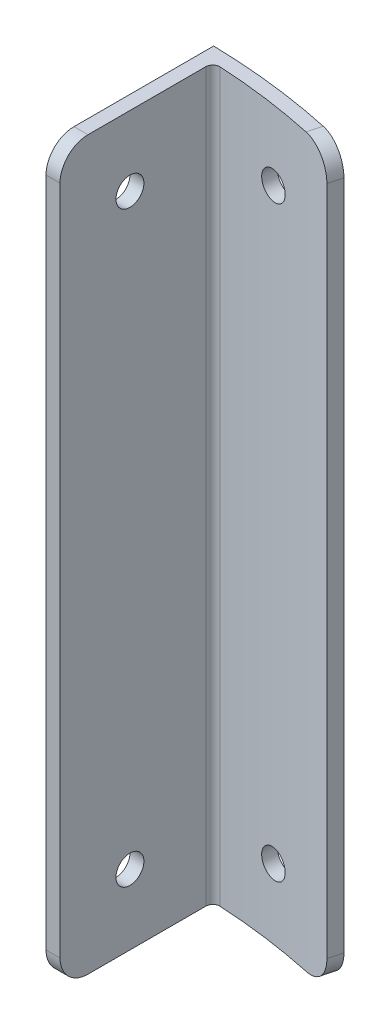
SolidWorks part; units mm, degrees
material "6061-T6 (SS)"
ref_plane "Front Plane" through (0, 0, 0) normal (0, 0, 1) x (1, 0, 0)
ref_plane "Top Plane" through (0, 0, 0) normal (0, 1, 0) x (1, 0, 0)
ref_plane "Right Plane" through (0, 0, 0) normal (1, 0, 0) x (0, 0, -1)
sketch "Sketch1" plane through (0, 0, 0) normal (0, 1, 0) x (1, 0, 0)
  line L0 (0, 149.225) -> (0, 0)
  line L1 (3.302, 111.125) -> (6.477, 111.125)
  line L2 (0, 149.225) -> (3.302, 149.225)
  line L3 (0, 149.225) -> (0, 111.125)
  line L4 (0, 111.125) -> (3.302, 111.125)
  line L5 (3.302, 149.225) -> (3.302, 111.125)
  line L6 (6.477, 111.125) -> (6.477, 145.9063)
  line L7 (0, 0) -> (37.6874, 144.3875)
  circle A0 centre (0, 0) radius 149.225
  circle A1 centre (0, 0) radius 146.05
  arc A2 (36.8855, 141.3155) -> (6.477, 145.9063) centre (0, 0) ccw
  circle A3 centre (0, 0) radius 146.05
  circle A4 centre (0, 0) radius 149.225
  dimension "D1" = 298.45
  dimension "D2" = 38.1
  dimension "D3" = 3.302
  dimension "D5" = 3.175
  dimension "D6" = 149.225
  dimension "D7" = 14.629
  dimension "D4" = 3.175
extrude "Boss-Extrude1" add sketch "Sketch1" along normal blind 165.1
fillet "Fillet1" radius 6.35 4 edges at (4.8895, 0, -111.125) (4.8895, 165.1, -111.125) (37.2865, 165.1, -142.8515) (37.2865, 0, -142.8515)
fillet "Fillet2" radius 1.5875 1 edges at (6.477, 82.55, -145.9063)
sketch "Sketch2" plane through (3.302, 0, 0) normal (-1, 0, 0) x (0, 0, 1)
  line L4 (-149.1885, 0) -> (-117.475, 0)
  line L5 (-111.125, 6.35) -> (-111.125, 158.75)
  line L6 (-117.475, 165.1) -> (-149.1885, 165.1)
  line L7 (-149.1885, 165.1) -> (-149.1885, 0)
  line L8 (-149.1885, 0) -> (-117.475, 0)
  line L9 (-111.125, 6.35) -> (-111.125, 158.75)
  line L10 (-117.475, 165.1) -> (-149.1885, 165.1)
  line L11 (-149.1885, 165.1) -> (-149.1885, 0)
  circle A0 centre (-127, 15.875) radius 3.175
  circle A1 centre (-127, 149.225) radius 3.175
  arc A2 (-117.475, 0) -> (-111.125, 6.35) centre (-117.475, 6.35) ccw
  arc A3 (-111.125, 158.75) -> (-117.475, 165.1) centre (-117.475, 158.75) ccw
  arc A4 (-117.475, 0) -> (-111.125, 6.35) centre (-117.475, 6.35) ccw
  arc A5 (-111.125, 158.75) -> (-117.475, 165.1) centre (-117.475, 158.75) ccw
  dimension "D2" = 6.35
  dimension "D3" = 6.35
  dimension "D4" = 15.875
  dimension "D5" = 15.875
  dimension "D6" = 15.875
  dimension "D7" = 133.35
  dimension "D1" = 0
extrude "Cut-Extrude1" cut sketch "Sketch2" against normal through all contours A1 | A0
ref_plane "Plane1" through (20.4947, 0, -146.788) normal (0.1383, 0, -0.9904) x (-0.9904, 0, -0.1383)
sketch "Sketch3" plane through (20.4947, 0, -146.788) normal (0.1383, 0, -0.9904) x (-0.9904, 0, -0.1383)
  line L4 (17.3595, 165.1) -> (-11.0369, 165.1)
  line L5 (-17.3595, 158.75) -> (-17.3595, 6.35)
  line L6 (-11.0369, 0) -> (17.3595, 0)
  line L7 (17.3595, 0) -> (17.3595, 165.1)
  line L8 (17.3595, 165.1) -> (-11.0369, 165.1)
  line L9 (-17.3595, 158.75) -> (-17.3595, 6.35)
  line L10 (-11.0369, 0) -> (17.3595, 0)
  line L11 (17.3595, 0) -> (17.3595, 165.1)
  circle A0 centre (-1.4845, 15.875) radius 3.175
  circle A1 centre (-1.4845, 149.225) radius 3.175
  spline S2 degree 3 poles (818.9016, -3746.326) (167.8329, -326.5656) (33.7061, 174.131) (-12.4726, 164.9382) (-12.673, 164.8881) (-13.0703, 164.7674) (-13.2678, 164.6966) (-13.8421, 164.4579) (-14.2051, 164.2631) (-14.8921, 163.8029) (-15.2173, 163.535) (-15.8, 162.9497) (-16.0615, 162.6303) (-16.4078, 162.1102) (-16.5153, 161.9299) (-16.7102, 161.5636) (-16.7982, 161.3766) (-17.0345, 160.8039) (-17.1558, 160.4045) (-29.8479, 96.4623) (930.648, -76.2088) (3928.8856, -482.342) knots -14.090794 -14.090794 -14.090794 -14.090794 0.125 0.125 0.1875 0.1875 0.25 0.25 0.375 0.375 0.5 0.5 0.625 0.625 0.6875 0.6875 0.75 0.75 0.875 0.875 20.234407 20.234407 20.234407 20.234407 only from (-11.0369, 165.1) to (-17.3595, 158.75)
  spline S3 degree 3 poles (3897.0223, 821.8265) (469.5052, 183.7472) (-26.3238, 51.153) (-17.1986, 4.9099) (-17.1487, 4.7087) (-17.0287, 4.31) (-16.9582, 4.1118) (-16.7209, 3.5352) (-16.5272, 3.1706) (-16.0695, 2.4805) (-15.803, 2.1537) (-15.2207, 1.568) (-14.9029, 1.3052) (-14.3851, 0.957) (-14.2056, 0.8489) (-13.8408, 0.6529) (-13.6546, 0.5644) (-13.0841, 0.3267) (-12.6863, 0.2048) (51.7013, -12.6885) (229.668, 973.7574) (664.6864, 3940.5188) knots -14.063055 -14.063055 -14.063055 -14.063055 0.125 0.125 0.1875 0.1875 0.25 0.25 0.375 0.375 0.5 0.5 0.625 0.625 0.6875 0.6875 0.75 0.75 0.875 0.875 20.435487 20.435487 20.435487 20.435487 only from (-17.3595, 6.35) to (-11.0369, 0)
  spline S4 degree 3 poles (-11.0369, 165.1) (-11.4551, 165.1) (-11.8661, 165.0589) (-12.4726, 164.9382) (-12.673, 164.8881) (-13.0703, 164.7674) (-13.2678, 164.6966) (-13.8421, 164.4579) (-14.2051, 164.2631) (-14.8921, 163.8029) (-15.2173, 163.535) (-15.8, 162.9497) (-16.0615, 162.6303) (-16.4078, 162.1102) (-16.5153, 161.9299) (-16.7102, 161.5636) (-16.7982, 161.3766) (-17.0345, 160.8039) (-17.1558, 160.4045) (-17.3186, 159.5841) (-17.3595, 159.1693) (-17.3595, 158.75) knots 0 0 0 0 0.125 0.125 0.1875 0.1875 0.25 0.25 0.375 0.375 0.5 0.5 0.625 0.625 0.6875 0.6875 0.75 0.75 0.875 0.875 1 1 1 1
  spline S5 degree 3 poles (-17.3595, 6.35) (-17.3595, 5.9307) (-17.3186, 5.5183) (-17.1986, 4.9099) (-17.1487, 4.7087) (-17.0287, 4.31) (-16.9582, 4.1118) (-16.7209, 3.5352) (-16.5272, 3.1706) (-16.0695, 2.4805) (-15.803, 2.1537) (-15.2207, 1.568) (-14.9029, 1.3052) (-14.3851, 0.957) (-14.2056, 0.8489) (-13.8408, 0.6529) (-13.6546, 0.5644) (-13.0841, 0.3267) (-12.6863, 0.2048) (-11.8686, 0.0411) (-11.4551, 0) (-11.0369, 0) knots 0 0 0 0 0.125 0.125 0.1875 0.1875 0.25 0.25 0.375 0.375 0.5 0.5 0.625 0.625 0.6875 0.6875 0.75 0.75 0.875 0.875 1 1 1 1
  dimension "D6" = 6.35
  dimension "D7" = 6.35
  dimension "D2" = 15.875
  dimension "D3" = 15.875
  dimension "D4" = 15.875
  dimension "D5" = 15.875
  dimension "D1" = 0
extrude "Cut-Extrude2" cut sketch "Sketch3" against normal up to next and the other way up to next contours A0 | A1
